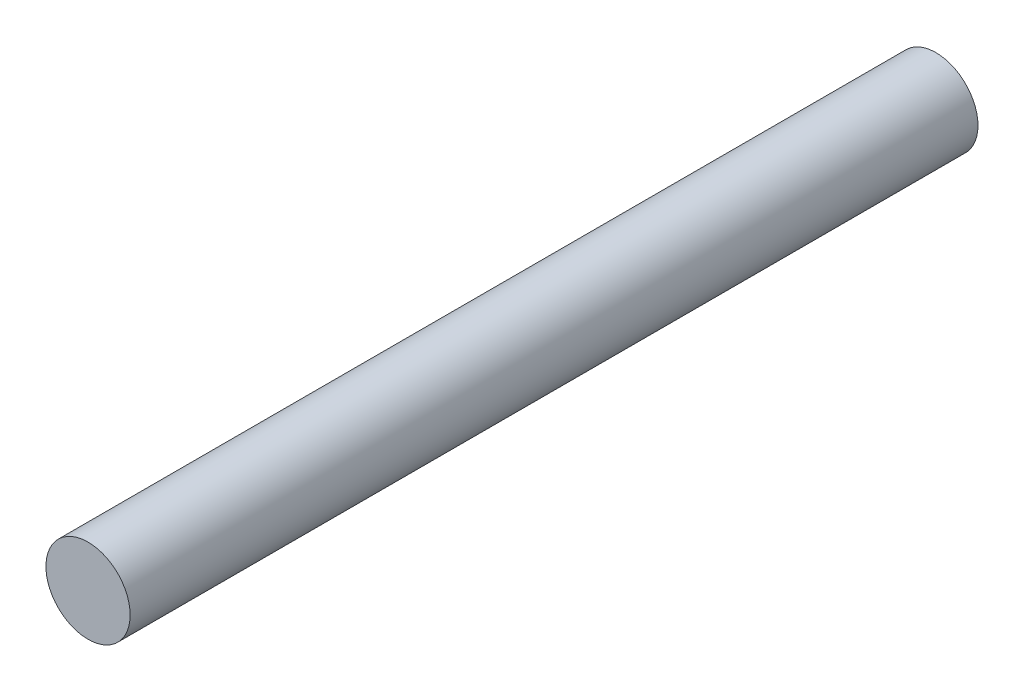
SolidWorks part; units mm, degrees
ref_plane "Front Plane" through (0, 0, 0) normal (0, 0, 1) x (1, 0, 0)
ref_plane "Top Plane" through (0, 0, 0) normal (0, 1, 0) x (1, 0, 0)
ref_plane "Right Plane" through (0, 0, 0) normal (1, 0, 0) x (0, 0, -1)
sketch "Sketch1" plane through (0, 0, 0) normal (0, 0, 1) x (1, 0, 0)
  circle A0 centre (0, 0) radius 3.725
  dimension "D1" = 7.45
extrude "Boss-Extrude1" add sketch "Sketch1" along normal blind 75
